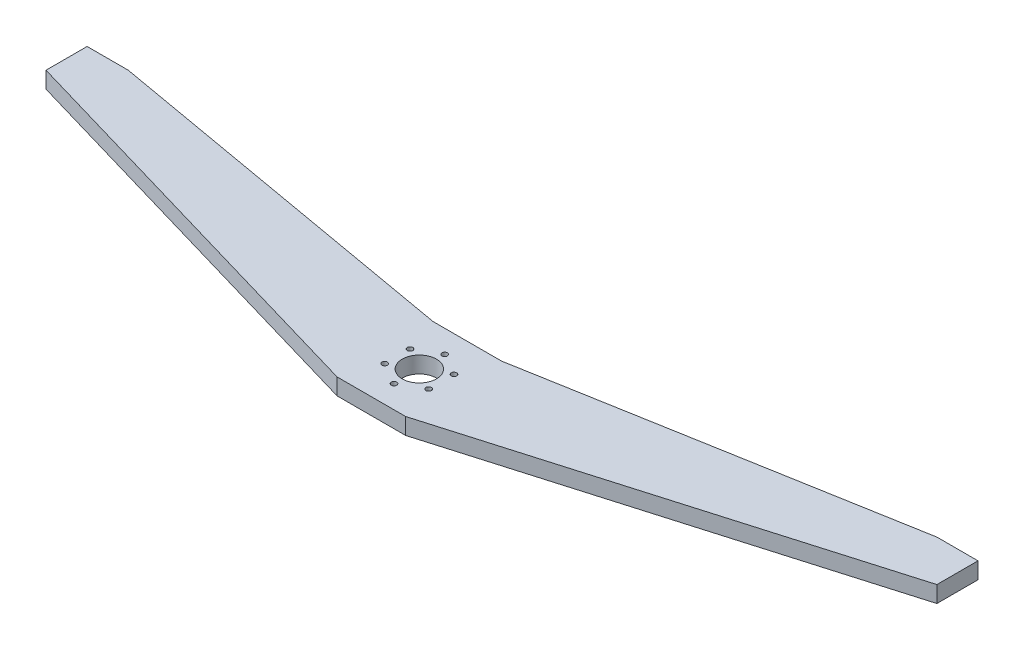
SolidWorks part; units mm, degrees
ref_plane "Front Plane" through (0, 0, 0) normal (0, 0, 1) x (1, 0, 0)
ref_plane "Top Plane" through (0, 0, 0) normal (0, 1, 0) x (1, 0, 0)
ref_plane "Right Plane" through (0, 0, 0) normal (1, 0, 0) x (0, 0, -1)
sketch "Sketch2" plane through (0, 0, 0) normal (0, 1, 0) x (1, 0, 0)
  line L0 (-318.2069, 87.6083) -> (-18.2069, 0)
  line L1 (-18.2069, 0) -> (31.7931, 0)
  line L2 (31.7931, 0) -> (331.7931, 87.6083)
  line L5 (31.7931, 70) -> (-18.2069, 70)
  line L8 (-318.2069, 87.6083) -> (-318.2069, 117.6083)
  line L9 (-318.2069, 117.6083) -> (-288.2069, 117.6083)
  line L10 (-288.2069, 117.6083) -> (-18.2069, 70)
  line L11 (331.7931, 87.6083) -> (331.7931, 117.6083)
  line L12 (331.7931, 117.6083) -> (301.7931, 117.6083)
  line L13 (301.7931, 117.6083) -> (31.7931, 70)
  point P6 (331.7931, 102.6083)
  dimension "D2" = 650
  dimension "D3" = 30
  dimension "D4" = 170
  dimension "D5" = 30
  dimension "D6" = 30
  dimension "D7" = 70
  dimension "D8" = 170
  dimension "D9" = 50
  dimension "D10" = 50
  dimension "D11" = 30
extrude "Boss-Extrude1" add sketch "Sketch2" along normal blind 12
sketch "Sketch3" plane through (-318.2069, 0, 0) normal (-1, 0, 0) x (0, 0, 1)
  line L3 (-117.6083, 12) -> (-117.6083, 0) construction
  circle A0 centre (-102.6083, 6) radius 6
  point P2 (-117.6083, 6)
  dimension "D2" = 12
  dimension "D1" = 15
sketch "Sketch4" plane through (0, 12, 0) normal (0, 1, 0) x (1, 0, 0)
  line L0 (31.7931, 70) -> (-18.2069, 70) construction
  circle A0 centre (6.7931, 35) radius 12.5
  circle A1 centre (6.7931, 35) radius 18.5 construction
  circle A2 centre (6.7931, 53.5) radius 2
  circle A3 centre (22.8146, 44.25) radius 2
  circle A4 centre (22.8146, 25.75) radius 2
  circle A5 centre (6.7931, 16.5) radius 2
  circle A6 centre (-9.2283, 25.75) radius 2
  circle A7 centre (-9.2283, 44.25) radius 2
  point P20 (6.7931, 35)
  dimension "D2" = 25
  dimension "D4" = 37
  dimension "D5" = 4
  dimension "D1" = 35
  dimension "D3" = 25
  dimension "D6" = 6
extrude "Cut-Extrude1" cut sketch "Sketch4" against normal blind 20
